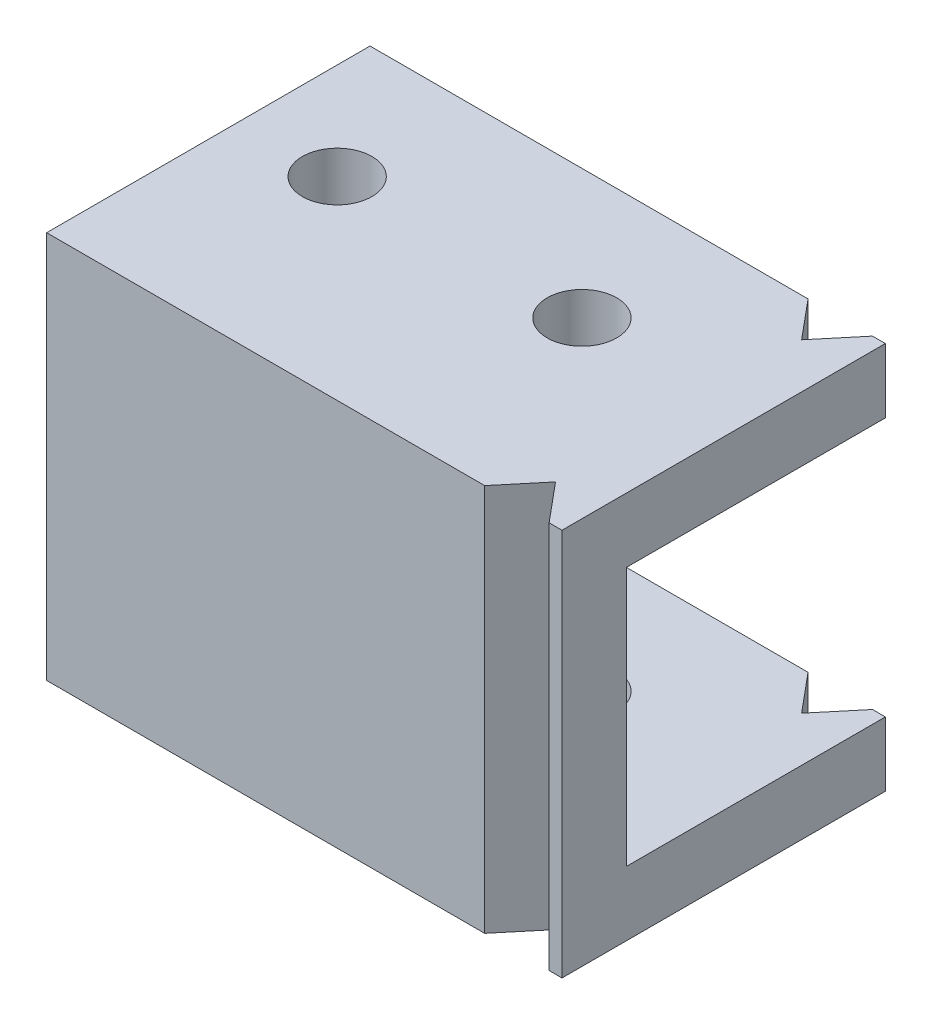
SolidWorks part; units mm, degrees
ref_plane "Front Plane" through (0, 0, 0) normal (0, 0, 1) x (1, 0, 0)
ref_plane "Top Plane" through (0, 0, 0) normal (0, 1, 0) x (1, 0, 0)
ref_plane "Right Plane" through (0, 0, 0) normal (1, 0, 0) x (0, 0, -1)
sketch "Sketch1" plane through (0, 0, 0) normal (1, 0, 0) x (0, 0, -1)
  line L0 (10.05, -10.05) -> (10.05, -15.05)
  line L1 (10.05, -10.05) -> (-10.05, -10.05) construction
  line L2 (10.05, -10.05) -> (10.05, 10.05) construction
  line L3 (10.05, 10.05) -> (-10.05, 10.05) construction
  line L4 (-10.05, -10.05) -> (-10.05, 10.05) construction
  line L5 (10.05, -10.05) -> (-10.05, 10.05) construction
  line L6 (10.05, 10.05) -> (-10.05, -10.05) construction
  line L7 (10.05, -15.05) -> (-15.05, -15.05) construction
  line L8 (10.05, -15.05) -> (10.05, 15.05) construction
  line L9 (10.05, 15.05) -> (-15.05, 15.05) construction
  line L10 (-15.05, -15.05) -> (-15.05, 15.05) construction
  line L11 (10.05, -15.05) -> (-15.05, 15.05) construction
  line L12 (10.05, 15.05) -> (-15.05, -15.05) construction
  line L13 (10.05, -15.05) -> (-15.05, -15.05)
  line L14 (-15.05, -15.05) -> (-15.05, 15.05)
  line L15 (-15.05, 15.05) -> (10.05, 15.05)
  line L16 (10.05, 15.05) -> (10.05, 10.05)
  line L17 (10.05, 10.05) -> (-10.05, 10.05)
  line L18 (-10.05, 10.05) -> (-10.05, -10.05)
  line L19 (-10.05, -10.05) -> (10.05, -10.05)
  line L20 (-10.05, 10.05) -> (-15.05, 10.05) construction
  point P0 (0, 0)
  point P6 (-2.5, 0)
  dimension "D1" = 20.1
  dimension "D2" = 5
extrude "Boss-Extrude1" add sketch "Sketch1" along normal blind 40
sketch "Sketch5" plane through (0, 15.05, 0) normal (0, 1, 0) x (1, 0, 0)
  line L0 (0, 0) -> (40, 0) construction
  line L1 (40, 10.05) -> (40, -15.05) construction
  line L2 (0, 10.05) -> (0, -15.05) construction
  line L3 (34, 10.05) -> (34, -15.05) construction
  line L4 (40, 10.05) -> (0, 10.05) construction
  line L5 (40, -15.05) -> (0, -15.05) construction
  line L9 (34, -15.05) -> (36.5, -12.05)
  line L10 (36.5, -12.05) -> (39, -15.05)
  line L11 (39, -15.05) -> (34, -15.05)
  line L12 (0, -2.5) -> (40, -2.5) construction
  line L17 (36.5, 7.05) -> (39, 10.05)
  line L18 (34, 10.05) -> (36.5, 7.05)
  line L19 (39, 10.05) -> (34, 10.05)
  circle A0 centre (7.5, 0) radius 2.7
  circle A1 centre (26.5, 0) radius 2.7
  point P25 (38.988, -15.05)
  dimension "D1" = 5.4
  dimension "D2" = 7.5
  dimension "D3" = 7.5
  dimension "D4" = 6
  dimension "D5" = 1
  dimension "D6" = 3
extrude "Cut-Extrude1" cut sketch "Sketch5" against normal through all
